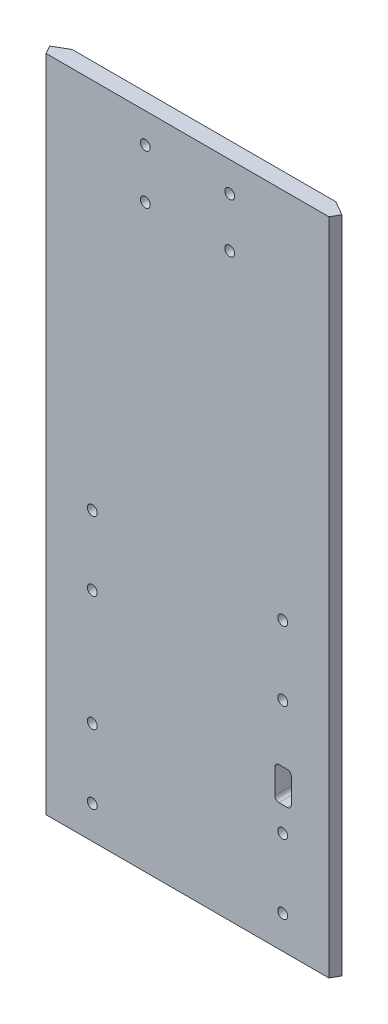
SolidWorks part; units mm, degrees
material "6061-T6 (SS)"
ref_plane "Front Plane" through (0, 0, 0) normal (0, 0, 1) x (1, 0, 0)
ref_plane "Top Plane" through (0, 0, 0) normal (0, 1, 0) x (1, 0, 0)
ref_plane "Right Plane" through (0, 0, 0) normal (1, 0, 0) x (0, 0, -1)
sketch "Sketch1" plane through (0, 0, 0) normal (0, 0, 1) x (1, 0, 0)
  line L0 (0, 101.6) -> (0, -152.4) construction
  line L1 (-50.8, 101.6) -> (50.8, 101.6)
  line L2 (-50.8, 101.6) -> (-50.8, -152.4)
  line L3 (-50.8, -152.4) -> (50.8, -152.4)
  line L4 (50.8, 101.6) -> (50.8, -152.4)
  point P0 (0, 0)
  point P7 (0, 0)
  dimension "D2" = 152.4
  dimension "D3" = 101.6
  dimension "D4" = 101.6
extrude "Boss-Extrude1" add sketch "Sketch1" along normal blind 6.35
sketch "Sketch2" plane through (0, 101.6, 0) normal (0, 1, 0) x (1, 0, 0)
  line L0 (-50.8, 0) -> (-61.7985, -6.35)
  line L1 (-61.7985, -6.35) -> (-50.8, -6.35)
  line L2 (0, 25.4532) -> (0, -25.9253) construction
  line L3 (50.8, -6.35) -> (-50.8, -6.35) construction
  line L4 (61.7985, -6.35) -> (50.8, -6.35)
  line L5 (50.8, 0) -> (61.7985, -6.35)
  line L6 (-50.8, 0) -> (-50.8, -6.35)
  line L7 (50.8, 0) -> (50.8, -6.35)
  dimension "D1" = 30
extrude "Boss-Extrude2" add sketch "Sketch2" against normal up to surface (254 mm away) up to face at (0, -152.4, 3.175)
sketch "Sketch4" plane through (0, 101.6, 0) normal (0, 1, 0) x (1, 0, 0)
  line L0 (56.2993, -3.175) -> (54.4662, -6.35)
  line L1 (61.7985, -6.35) -> (50.8, 0) construction
  line L2 (61.7985, -6.35) -> (-61.7985, -6.35) construction
  line L3 (50.8, 0) -> (56.2993, -3.175) construction
  line L4 (56.2993, -3.175) -> (61.7985, -6.35) construction
  line L5 (0, -37.5209) -> (0, 30.0282) construction
  line L6 (56.2993, -3.175) -> (61.7985, -6.35)
  line L7 (61.7985, -6.35) -> (54.4662, -6.35)
  line L8 (-61.7985, -6.35) -> (-54.4662, -6.35)
  line L9 (-56.2993, -3.175) -> (-61.7985, -6.35)
  line L10 (-56.2993, -3.175) -> (-54.4662, -6.35)
extrude "Cut-Extrude2" cut sketch "Sketch4" against normal through all
sketch "Sketch5" plane through (0, 0, 6.35) normal (0, 0, 1) x (1, 0, 0)
  line L0 (-54.4662, -152.4) -> (54.4662, -152.4) construction
  line L3 (-56.2993, -152.4) -> (-56.2993, 101.6) construction
  circle A8 centre (-36.6862, -41.91) radius 1.905
  circle A9 centre (36.6862, -41.91) radius 1.905
  circle A18 centre (36.6862, -68.58) radius 1.905
  circle A19 centre (36.6862, -113.03) radius 1.905
  circle A20 centre (36.6862, -139.7) radius 1.905
  circle A21 centre (-36.6862, -139.7) radius 1.905
  circle A22 centre (-36.6862, -113.03) radius 1.905
  circle A23 centre (-36.6862, -68.58) radius 1.905
  dimension "D8" = 3.81
  dimension "D1" = 26.67
  dimension "D2" = 26.67
  dimension "D3" = 73.3723
  dimension "D4" = 12.7
  dimension "D5" = 44.45
  dimension "D6" = 19.6131
extrude "Cut-Extrude3" cut sketch "Sketch5" against normal through all
cosmetic thread "Cosmetic Thread25" parameters "D2"=4.826
cosmetic thread "Cosmetic Thread26" parameters "D2"=4.826
cosmetic thread "Cosmetic Thread27" parameters "D2"=4.826
cosmetic thread "Cosmetic Thread28" parameters "D2"=4.826
cosmetic thread "Cosmetic Thread29" parameters "D2"=4.826
cosmetic thread "Cosmetic Thread30" parameters "D2"=4.826
cosmetic thread "Cosmetic Thread31" parameters "D2"=4.826
cosmetic thread "Cosmetic Thread32" parameters "D2"=4.826
sketch "Sketch6" plane through (0, 0, 6.35) normal (0, 0, 1) x (1, 0, 0)
  line L1 (54.4662, 101.6) -> (-54.4662, 101.6) construction
  line L2 (0, 192.8724) -> (0, -81.2612) construction
  circle A0 centre (-16.256, 90.17) radius 1.905
  circle A1 centre (16.256, 90.17) radius 1.905
  circle A2 centre (16.256, 71.12) radius 1.905
  circle A3 centre (-16.256, 71.12) radius 1.905
  dimension "D1" = 3.81
  dimension "D2" = 19.05
  dimension "D3" = 16.256
  dimension "D4" = 19.05
  dimension "D5" = 16.256
  dimension "D6" = 11.43
extrude "Cut-Extrude4" cut sketch "Sketch6" against normal through all
cosmetic thread "Cosmetic Thread33" parameters "D2"=4.826
cosmetic thread "Cosmetic Thread34" parameters "D2"=4.826
cosmetic thread "Cosmetic Thread35" parameters "D2"=4.826
cosmetic thread "Cosmetic Thread36" parameters "D2"=4.826
sketch "Sketch9" plane through (0, 0, 6.35) normal (0, 0, 1) x (1, 0, 0)
  line L0 (33.6382, -90.805) -> (33.6382, -103.505) construction
  line L3 (33.6382, -90.805) -> (33.6382, -103.505)
  line L4 (33.6382, -103.505) -> (39.9882, -103.505)
  line L5 (39.9882, -103.505) -> (39.9882, -90.805)
  line L6 (33.6382, -90.805) -> (39.9882, -90.805)
  dimension "D1" = 6.35
extrude "Cut-Extrude5" cut sketch "Sketch9" against normal through all
fillet "Fillet1" radius 1.5875 4 edges at (33.6382, -90.805, 3.175) (39.9882, -103.505, 3.175) (33.6382, -103.505, 3.175) (39.9882, -90.805, 3.175)
